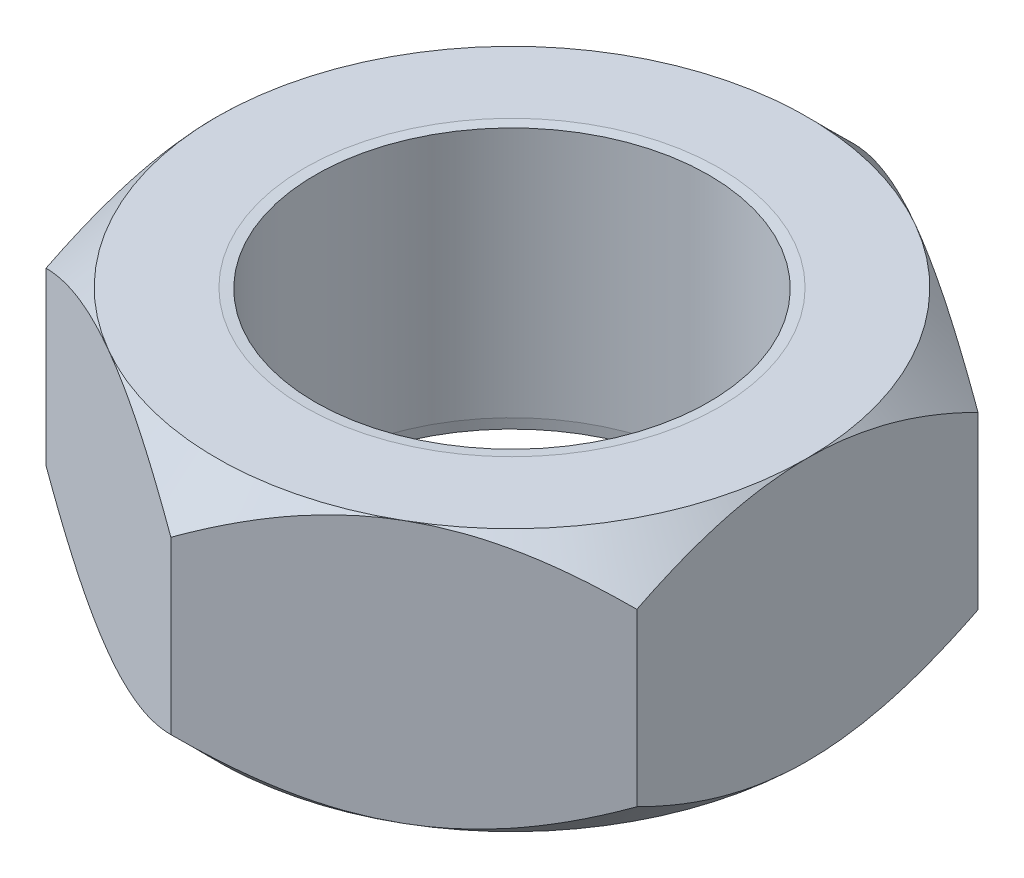
SolidWorks part; units mm, degrees
ref_plane "Front Plane" through (0, 0, 0) normal (0, 0, 1) x (1, 0, 0)
ref_plane "Top Plane" through (0, 0, 0) normal (0, 1, 0) x (1, 0, 0)
ref_plane "Right Plane" through (0, 0, 0) normal (1, 0, 0) x (0, 0, -1)
sketch "Sketch1" plane through (0, 0, 0) normal (0, 1, 0) x (1, 0, 0)
  line L1 (0, 8.2562) -> (-7.1501, 4.1281)
  line L2 (-7.1501, 4.1281) -> (-7.1501, -4.1281)
  line L3 (-7.1501, -4.1281) -> (0, -8.2562)
  line L4 (0, -8.2562) -> (7.1501, -4.1281)
  line L5 (7.1501, -4.1281) -> (7.1501, 4.1281)
  line L6 (7.1501, 4.1281) -> (0, 8.2562)
  circle A0 centre (0, 0) radius 7.1501 construction
  point P1 (0, 0)
  dimension "D1" = 14.3002
extrude "Boss-Extrude1" add sketch "Sketch1" along normal blind 6.35
sketch "Sketch2" plane through (0, 6.35, 0) normal (0, 1, 0) x (1, 0, 0)
  circle A0 centre (0, 0) radius 4.7625
  dimension "D1" = 9.525
extrude "Cut-Extrude1" cut sketch "Sketch2" against normal through all
cosmetic thread "Cosmetic Thread1" parameters "D2"=11.1125
chamfer "Chamfer2" distance 0.254 angle 5 1 edges at (0, 6.35, 4.7625)
chamfer "Chamfer3" distance 0.254 angle 5 1 edges at (0, 0, 4.7625)
sketch "Sketch3" plane through (0, 6.35, 0) normal (0, 1, 0) x (1, 0, 0)
  circle A0 centre (0, 0) radius 7.1501
extrude "Cut-Extrude2" cut sketch "Sketch3" against normal blind 6.35 draft 45 flip side to cut
sketch "Sketch4" plane through (0, 0, 0) normal (0, -1, 0) x (1, 0, 0)
  circle A0 centre (0, 0) radius 7.1501
extrude "Cut-Extrude3" cut sketch "Sketch4" against normal blind 6.35 draft 45 flip side to cut
